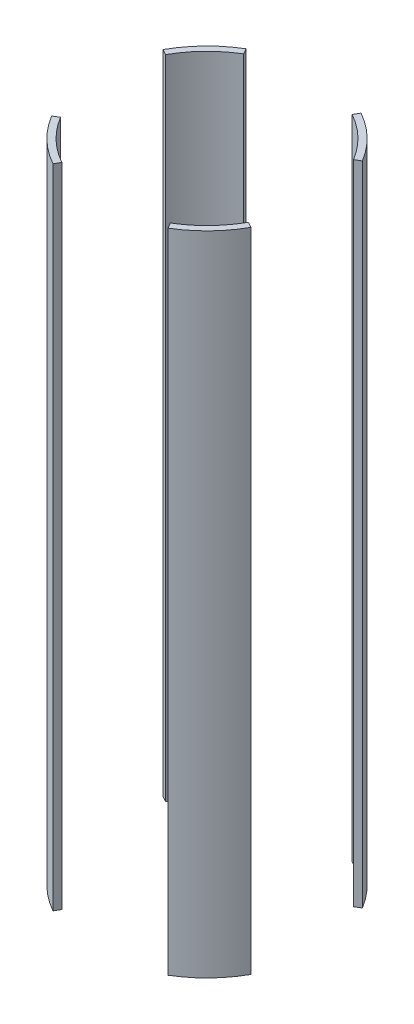
SolidWorks part; units mm, degrees
ref_plane "Front Plane" through (0, 0, 0) normal (0, 0, 1) x (1, 0, 0)
ref_plane "Top Plane" through (0, 0, 0) normal (0, 1, 0) x (1, 0, 0)
ref_plane "Right Plane" through (0, 0, 0) normal (1, 0, 0) x (0, 0, -1)
sketch "Sketch2" plane through (0, 0, 0) normal (0, 1, 0) x (1, 0, 0)
  circle A0 centre (0, 0) radius 88.9
  circle A1 centre (0, 0) radius 83.82
  dimension "D1" = 177.8
  dimension "D2" = 167.64
extrude "Boss-Extrude1" add sketch "Sketch2" along normal mid plane 508
sketch "Sketch3" plane through (0, 0, 0) normal (0, 1, 0) x (1, 0, 0)
  line L0 (0, 0) -> (169.6618, 101.6776)
  line L1 (-58.1167, 96.9749) -> (0, 0)
  line L2 (0, 0) -> (53.9, 96.9749)
  line L3 (53.9, 96.9749) -> (-58.1167, 96.9749)
  line L4 (0, 0) -> (70.9917, -118.4586)
  line L5 (70.9917, -118.4586) -> (-65.8409, -118.4586)
  line L6 (-65.8409, -118.4586) -> (0, 0)
  line L7 (169.6618, 101.6776) -> (169.6618, -94.3004)
  line L8 (169.6618, -94.3004) -> (0, 0)
  line L9 (0, 0) -> (-123.7413, 68.7771)
  line L10 (-123.7413, 68.7771) -> (-123.7413, -74.1577)
  line L11 (-123.7413, -74.1577) -> (0, 0)
  dimension "D1" = 60
  dimension "D2" = 60
  dimension "D3" = 60
  dimension "D4" = 60
  dimension "D5" = 30
  dimension "D6" = 30
extrude "Cut-Extrude1" cut sketch "Sketch3" against normal through all both and the other way through all contours L8 L7 L0 | L2 L3 L1 | L10 L11 L9 | L6 L5 L4
equation "\"D1@Boss-Extrude1\"=3*12"
